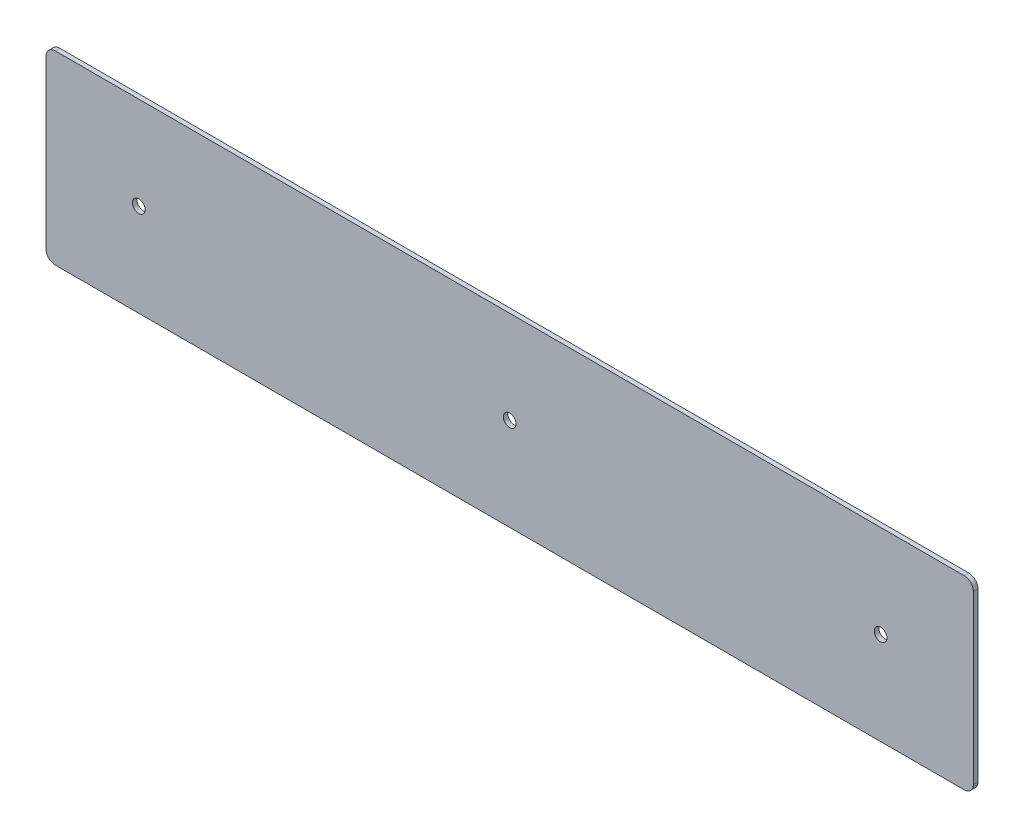
SolidWorks part; units mm, degrees
ref_plane "Front Plane" through (0, 0, 0) normal (0, 0, 1) x (1, 0, 0)
ref_plane "Top Plane" through (0, 0, 0) normal (0, 1, 0) x (1, 0, 0)
ref_plane "Right Plane" through (0, 0, 0) normal (1, 0, 0) x (0, 0, -1)
sketch "Sketch1" plane through (0, 0, 0) normal (0, 0, 1) x (1, 0, 0)
  line L1 (-158.75, 31.75) -> (158.75, 31.75)
  line L2 (-158.75, 31.75) -> (-158.75, -31.75)
  line L3 (-158.75, -31.75) -> (158.75, -31.75)
  line L4 (158.75, 31.75) -> (158.75, -31.75)
  line L5 (-158.75, 31.75) -> (158.75, -31.75) construction
  line L6 (-158.75, -31.75) -> (158.75, 31.75) construction
  circle A0 centre (0, 0) radius 2.1828
  circle A1 centre (127, 0) radius 2.1828
  circle A2 centre (-127, 0) radius 2.1828
  point P0 (0, 0)
  point P12 (0, 0)
  dimension "D5" = 4.3656
  dimension "D6" = 4.3656
  dimension "D7" = 4.3656
  dimension "D1" = 63.5
  dimension "D2" = 317.5
  dimension "D3" = 127
  dimension "D4" = 127
extrude "Boss-Extrude1" add sketch "Sketch1" along normal mid plane 1.5875
fillet "Fillet1" radius 3.175 4 edges at (-158.75, -31.75, 0) (-158.75, 31.75, 0) (158.75, -31.75, 0) (158.75, 31.75, 0)
